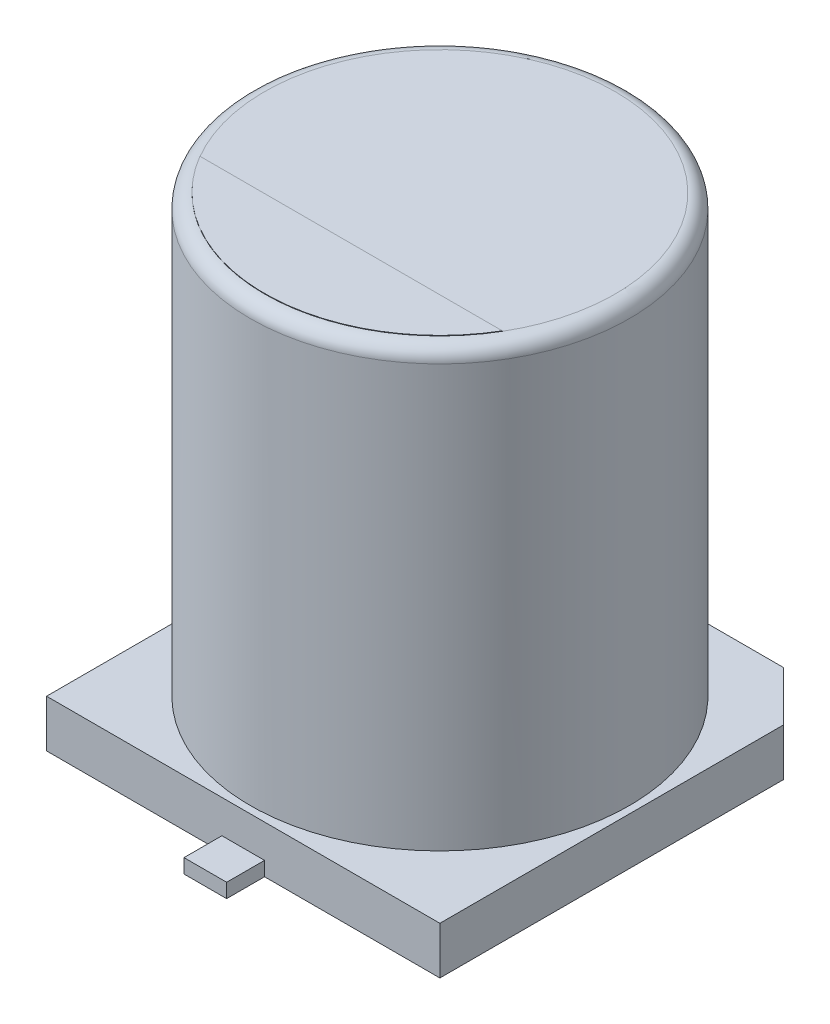
SolidWorks part; units mm, degrees
ref_plane "Front Plane" through (0, 0, 0) normal (0, 0, 1) x (1, 0, 0)
ref_plane "Top Plane" through (0, 0, 0) normal (0, 1, 0) x (1, 0, 0)
ref_plane "Right Plane" through (0, 0, 0) normal (1, 0, 0) x (0, 0, -1)
sketch "Sketch2" plane through (0, 0, 0) normal (0, 1, 0) x (1, 0, 0)
  line L0 (0, 0) -> (0, 2.085) construction
  line L1 (0, 0) -> (2.9643, 0) construction
  line L2 (4.15, -4.15) -> (-4.15, -4.15)
  line L3 (-4.15, -4.15) -> (-4.15, 3.1)
  line L4 (-4.15, 3.1) -> (-3.1, 4.15)
  line L5 (-3.1, 4.15) -> (3.1, 4.15)
  line L6 (3.1, 4.15) -> (4.15, 3.1)
  line L7 (4.15, 3.1) -> (4.15, -4.15)
  line L8 (0, -4.15) -> (0, -0.9795) construction
  line L9 (0, 4.15) -> (0, 2.1922) construction
  line L10 (-0.2934, -4.15) -> (-0.2934, 4.15) construction
  line L11 (-0.2934, 0) -> (-0.8682, 0) construction
  dimension "D1" = 8.3
  dimension "D2" = 8.3
  dimension "D3" = 6.2
extrude "Boss-Extrude1" add sketch "Sketch2" along normal blind 1
sketch "Sketch3" plane through (0, 0, 0) normal (0, 1, 0) x (1, 0, 0)
  circle A0 centre (0, 0) radius 4
  dimension "D1" = 8
extrude "Boss-Extrude2" add sketch "Sketch3" along normal blind 10.2 contours A0
fillet "Fillet1" radius 0.3 1 edges at (0, 10.2, 4)
sketch "Sketch4" plane through (0, 0, 0) normal (0, 1, 0) x (1, 0, 0)
  line L0 (0, 0) -> (0.4492, 0) construction
  line L1 (0.45, 4.95) -> (-0.45, 4.95)
  line L2 (0.45, -1.55) -> (-0.45, -1.55)
  line L3 (0.45, -1.55) -> (0.45, -4.95)
  line L4 (0.45, -4.95) -> (-0.45, -4.95)
  line L5 (-0.45, -1.55) -> (-0.45, -4.95)
  line L6 (0.45, -1.55) -> (-0.45, -4.95) construction
  line L7 (0.45, -4.95) -> (-0.45, -1.55) construction
  line L8 (-0.45, 1.55) -> (-0.45, 4.95)
  line L9 (0.45, 1.55) -> (-0.45, 1.55)
  line L10 (0.45, 1.55) -> (0.45, 4.95)
  line L11 (0.45, 4.95) -> (-0.45, 1.55) construction
  line L12 (0.45, 1.55) -> (-0.45, 4.95) construction
  point P1 (0, -3.25)
  point P12 (0, 3.25)
  dimension "D1" = 0.9
  dimension "D2" = 3.4
  dimension "D3" = 3.1
extrude "Boss-Extrude3" add sketch "Sketch4" along normal blind 0.3
ref_plane "Plane1" through (0, 10.2, 0) normal (0, 1, 0) x (1, 0, 0)
sketch "Sketch5" plane through (0, 10.2, 0) normal (0, 1, 0) x (1, 0, 0)
  line L0 (-3.1907, -1.8734) -> (3.1907, -1.8734)
  circle A0 centre (0, 0) radius 3.7 construction
  arc A1 (-3.1907, -1.8734) -> (3.1907, -1.8734) centre (0, 0) ccw
extrude "Boss-Extrude4" add sketch "Sketch5" along normal blind 0.01
